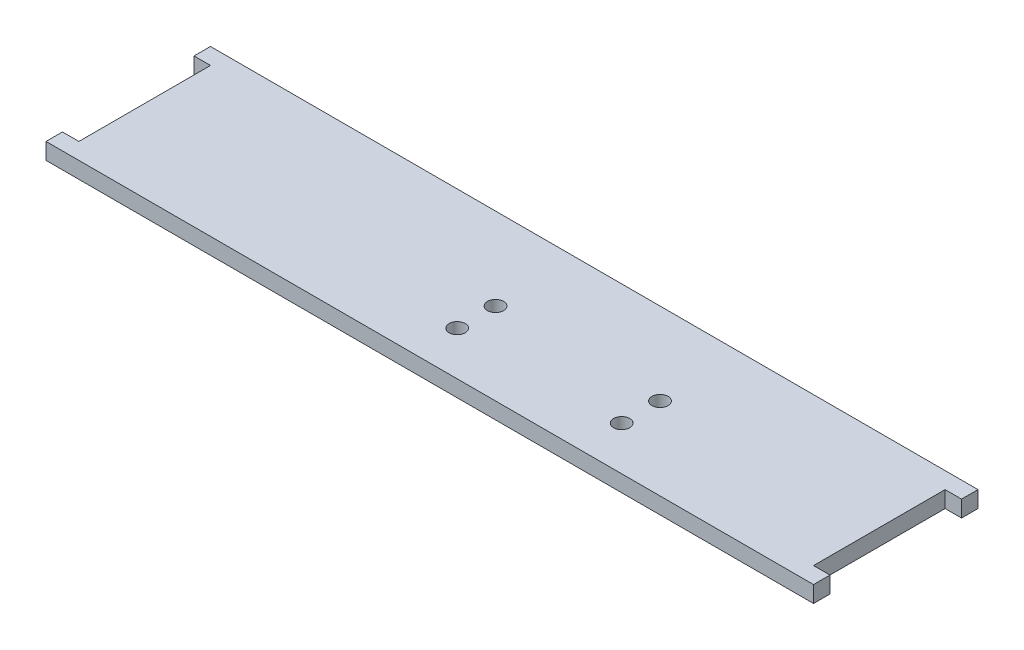
SolidWorks part; units mm, degrees
ref_plane "Front Plane" through (0, 0, 0) normal (0, 0, 1) x (1, 0, 0)
ref_plane "Top Plane" through (0, 0, 0) normal (0, 1, 0) x (1, 0, 0)
ref_plane "Right Plane" through (0, 0, 0) normal (1, 0, 0) x (0, 0, -1)
sketch "Sketch1" plane through (0, 0, 0) normal (0, 1, 0) x (1, 0, 0)
  line L1 (-70, -15) -> (70, -15)
  line L2 (-70, -15) -> (-70, 15)
  line L3 (-70, 15) -> (70, 15)
  line L4 (70, -15) -> (70, 15)
  line L5 (-70, -15) -> (70, 15) construction
  line L6 (-70, 15) -> (70, -15) construction
  point P0 (0, 0)
  dimension "D1" = 30
  dimension "D2" = 140
extrude "Boss-Extrude1" add sketch "Sketch1" along normal blind 3
sketch "Sketch2" plane through (0, 3, 0) normal (0, 1, 0) x (1, 0, 0)
  line L0 (-70, 12) -> (-67, 12)
  line L1 (-70, 15) -> (-70, -15) construction
  line L2 (-67, 12) -> (-67, -12)
  line L3 (-67, -12) -> (-70, -12)
  line L4 (-70, -12) -> (-70, 12)
  line L5 (0, -1.65) -> (0, 1.65) construction
  line L6 (70, -12) -> (70, 12)
  line L7 (67, -12) -> (70, -12)
  line L8 (70, 12) -> (67, 12)
  line L9 (67, 12) -> (67, -12)
  point P5 (-70, 0)
  point P7 (-70, 0)
  dimension "D1" = 24
  dimension "D2" = 3
extrude "Cut-Extrude1" cut sketch "Sketch2" against normal blind 3
sketch "Sketch3" plane through (0, 3, 0) normal (0, 1, 0) x (1, 0, 0)
  line L0 (67, 12) -> (67, -12) construction
  line L3 (-70, -15) -> (70, -15) construction
  circle A0 centre (-3, 0) radius 1.47
  circle A1 centre (-3, -7) radius 1.47
  circle A2 centre (27, 0) radius 1.47
  circle A3 centre (27, -7) radius 1.47
  dimension "D1" = 2.94
  dimension "D4" = 40
  dimension "D5" = 15
  dimension "D2" = 30
  dimension "D3" = 7
extrude "Cut-Extrude2" cut sketch "Sketch3" against normal blind 3
